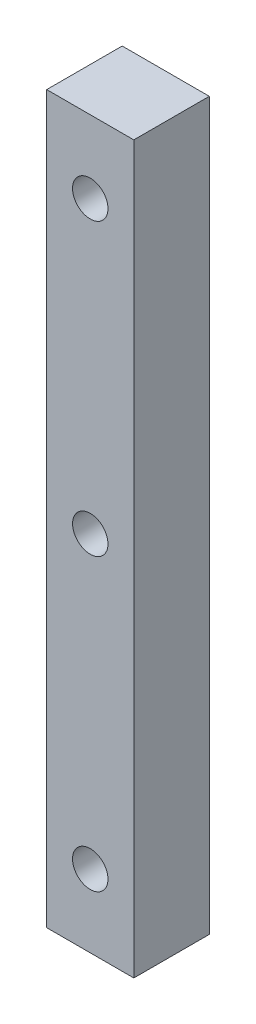
SolidWorks part; units mm, degrees
ref_plane "Front Plane" through (0, 0, 0) normal (0, 0, 1) x (1, 0, 0)
ref_plane "Top Plane" through (0, 0, 0) normal (0, 1, 0) x (1, 0, 0)
ref_plane "Right Plane" through (0, 0, 0) normal (1, 0, 0) x (0, 0, -1)
sketch "Sketch1" plane through (0, 0, 0) normal (0, 1, 0) x (1, 0, 0)
  line L1 (0, 0) -> (3, 0)
  line L2 (0, 0) -> (0, 2.6)
  line L3 (0, 2.6) -> (3, 2.6)
  line L4 (3, 0) -> (3, 2.6)
  dimension "D1" = 3
  dimension "D2" = 2.6
extrude "Boss-Extrude1" add sketch "Sketch1" along normal blind 25
sketch "Sketch2" plane through (0, 0, 0) normal (0, 0, 1) x (1, 0, 0)
  line L0 (0, 25) -> (3, 25) construction
  circle A0 centre (1.5, 22.5) radius 0.61
  circle A1 centre (1.5, 12.5) radius 0.61
  circle A2 centre (1.5, 2.5) radius 0.61
  point P6 (0, 0)
  point P7 (1.5, 22.2662)
  point P8 (1.5431, 23.4702)
  point P9 (1.5913, 22.4588)
  point P10 (0, 0)
  point P13 (1.5, 25)
  dimension "D1" = 1.22
  dimension "D2" = 10
  dimension "D3" = 2.5
  dimension "D4" = 10
extrude "Cut-Extrude1" cut sketch "Sketch2" against normal through all
